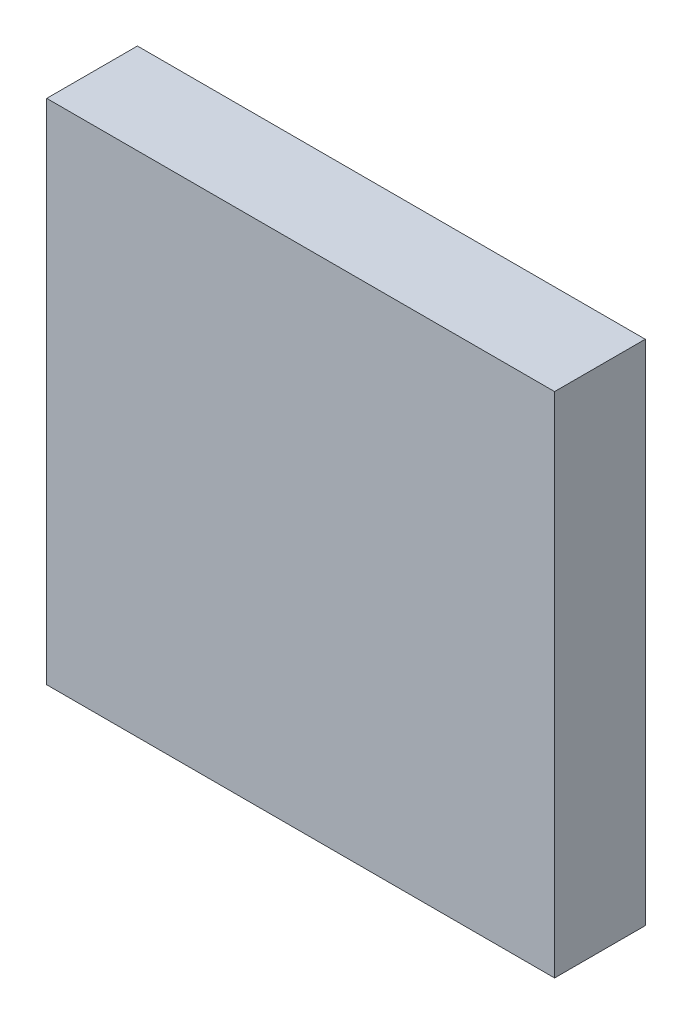
SolidWorks part; units mm, degrees
material "Glass"
ref_plane "Front Plane" through (0, 0, 0) normal (0, 0, 1) x (1, 0, 0)
ref_plane "Top Plane" through (0, 0, 0) normal (0, 1, 0) x (1, 0, 0)
ref_plane "Right Plane" through (0, 0, 0) normal (1, 0, 0) x (0, 0, -1)
sketch "Sketch1" plane through (0, 0, 0) normal (0, 0, 1) x (1, 0, 0)
  line L1 (-3.5, -3.5) -> (3.5, -3.5)
  line L2 (-3.5, -3.5) -> (-3.5, 3.5)
  line L3 (-3.5, 3.5) -> (3.5, 3.5)
  line L4 (3.5, -3.5) -> (3.5, 3.5)
  line L5 (-3.5, -3.5) -> (3.5, 3.5) construction
  line L6 (-3.5, 3.5) -> (3.5, -3.5) construction
  point P0 (0, 0)
  dimension "D1" = 7
  dimension "D2" = 7
extrude "Boss-Extrude1" add sketch "Sketch1" along normal blind 1.25
